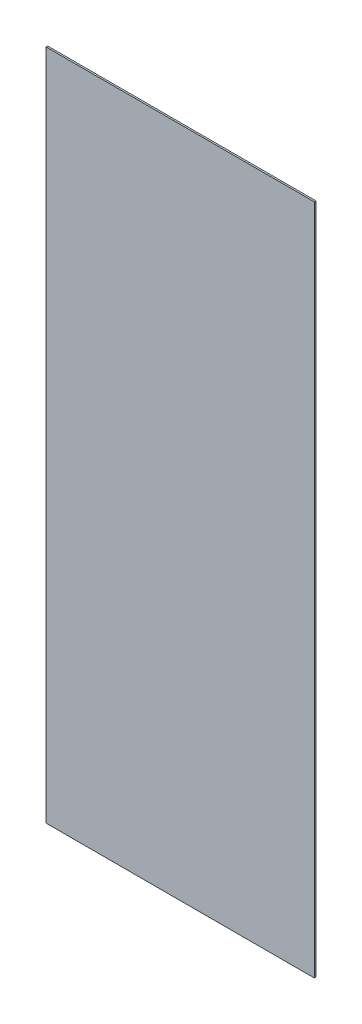
SolidWorks part; units mm, degrees
material "Hexcel AS4C (3000 Filaments)"
ref_plane "Front" through (0, 0, 0) normal (0, 0, 1) x (1, 0, 0)
ref_plane "Top" through (0, 0, 0) normal (0, 1, 0) x (1, 0, 0)
ref_plane "Right" through (0, 0, 0) normal (1, 0, 0) x (0, 0, -1)
sketch "Sketch1" plane through (0, 0, 0) normal (0, 0, 1) x (1, 0, 0)
  line L0 (-3.4839, -67.2437) -> (46.5161, -67.2437) construction
  line L1 (-60.4839, 315.8769) -> (103.5161, 315.8769)
  line L2 (-60.4839, 315.8769) -> (-60.4839, -95.1231)
  line L3 (-60.4839, -95.1231) -> (103.5161, -95.1231)
  line L4 (103.5161, 315.8769) -> (103.5161, -95.1231)
  line L5 (-3.4839, -90.5771) -> (-3.4839, -67.2437) construction
  dimension "D1" = 411
  dimension "D2" = 164
  dimension "D3" = 27.8793
  dimension "D4" = 57
extrude "Boss-Extrude1" add sketch "Sketch1" along normal blind 1
